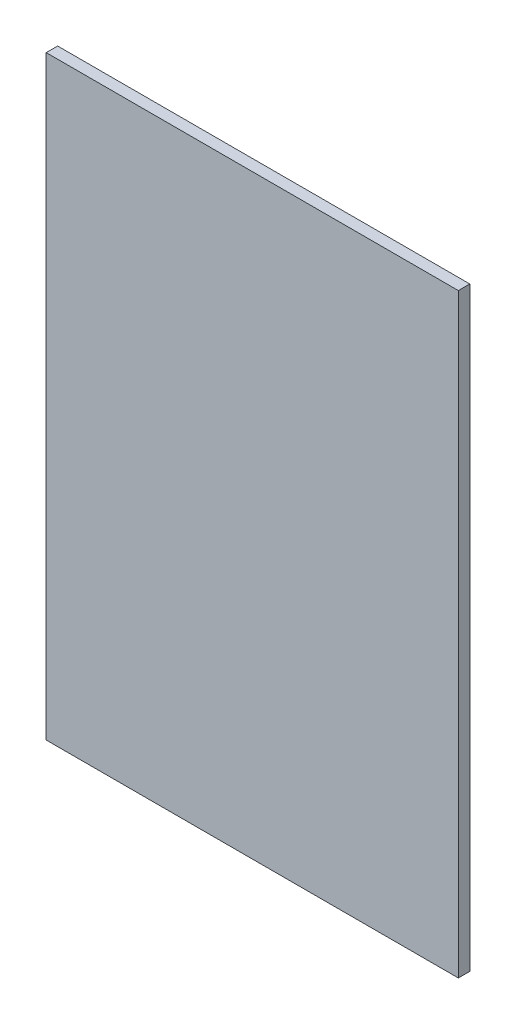
SolidWorks part; units mm, degrees
ref_plane "Plan de face" through (0, 0, 0) normal (0, 0, 1) x (1, 0, 0)
ref_plane "Plan de dessus" through (0, 0, 0) normal (0, 1, 0) x (1, 0, 0)
ref_plane "Plan de droite" through (0, 0, 0) normal (1, 0, 0) x (0, 0, -1)
sketch "Esquisse1" plane through (0, 0, 0) normal (0, 0, 1) x (1, 0, 0)
  line L1 (-115.4615, 454.4085) -> (244.5385, 454.4085)
  line L2 (-115.4615, 454.4085) -> (-115.4615, -65.5915)
  line L3 (-115.4615, -65.5915) -> (244.5385, -65.5915)
  line L4 (244.5385, 454.4085) -> (244.5385, -65.5915)
  dimension "D1" = 360
  dimension "D2" = 520
extrude "Boss.-Extru.1" add sketch "Esquisse1" along normal blind 10
equation "\"LargeurPlacard\"=360"
equation "\"D1@Esquisse1\"=\"LargeurPlacard\""
equation "\"ProfondeurPlacard\"=520"
equation "\"D2@Esquisse1\"=\"ProfondeurPlacard\""
